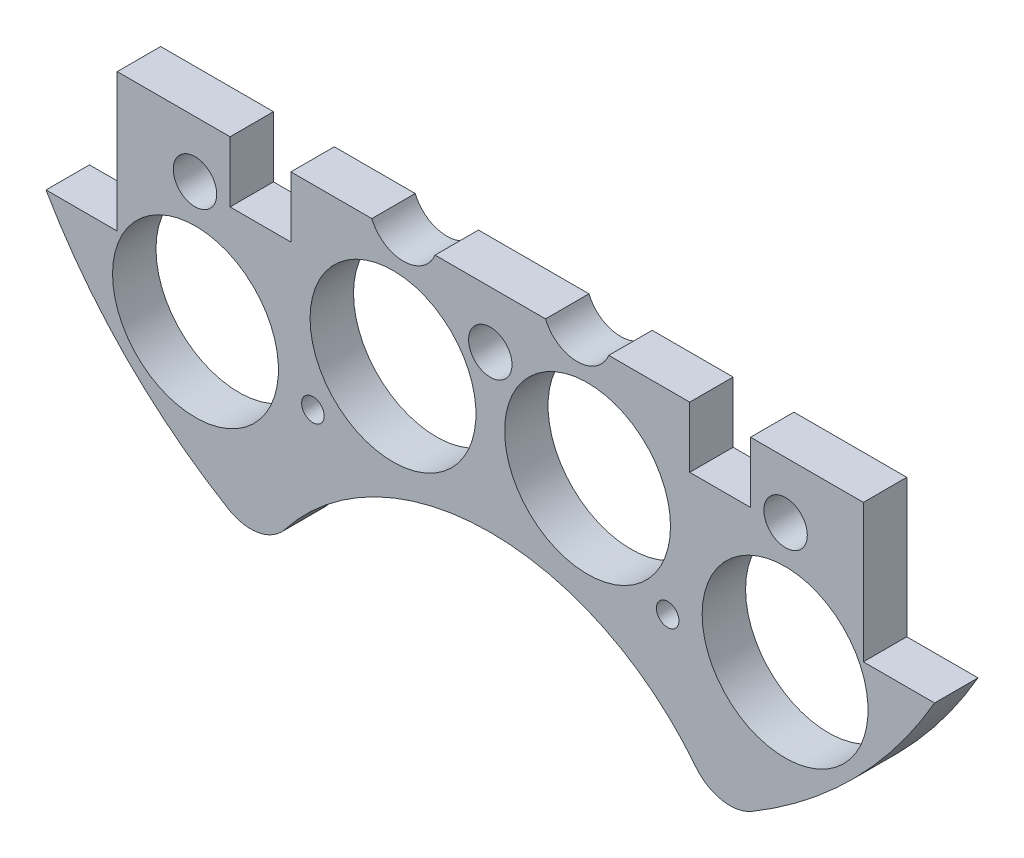
SolidWorks part; units mm, degrees
ref_plane "Front Plane" through (0, 0, 0) normal (0, 0, 1) x (1, 0, 0)
ref_plane "Top Plane" through (0, 0, 0) normal (0, 1, 0) x (1, 0, 0)
ref_plane "Right Plane" through (0, 0, 0) normal (1, 0, 0) x (0, 0, -1)
sketch "Sketch1" plane through (0, 0, 0) normal (0, 0, 1) x (1, 0, 0)
  line L0 (0, 0) -> (-82.1241, 0) construction
  line L1 (0, 0) -> (0, 95.6219) construction
  line L3 (-64.9644, 37.338) -> (-54.5504, 37.338)
  line L5 (-64.9644, -37.338) -> (-54.5504, -37.338)
  line L6 (-54.5504, 37.338) -> (-54.5504, -37.338)
  line L7 (64.9644, -37.338) -> (54.5504, -37.338)
  line L8 (64.9644, 37.338) -> (54.5504, 37.338)
  line L9 (54.5504, 37.338) -> (54.5504, -37.338)
  arc A0 (-64.9644, -37.338) -> (64.9644, -37.338) centre (0, 0) ccw
  circle A1 centre (-46.482, 11.049) radius 1.651
  circle A2 centre (-21.0833, 10.795) radius 1.651
  circle A3 centre (-21.0833, -10.795) radius 1.651
  circle A4 centre (-46.482, -11.049) radius 1.651
  circle A5 centre (46.482, -11.049) radius 1.651
  circle A6 centre (21.0833, -10.795) radius 1.651
  circle A7 centre (21.0833, 10.795) radius 1.651
  circle A8 centre (46.482, 11.049) radius 1.651
  arc A9 (64.9644, 37.338) -> (-64.9644, 37.338) centre (0, 0) ccw
  dimension "D2" = 3.302
  dimension "D3" = 3.302
  dimension "D4" = 25.4
  dimension "D5" = 10.795
  dimension "D10" = 46.482
  dimension "D6" = 74.676
  dimension "D7" = 10.414
  dimension "D8" = 74.93
  dimension "D9" = 74.93
  dimension "D11" = 37.338
extrude "Boss-Extrude2" add sketch "Sketch1" along normal blind 6.35
sketch "Sketch2" plane through (0, 0, 6.35) normal (0, 0, 1) x (1, 0, 0)
  line L0 (0, 68.58) -> (0, 55.88) construction
  line L1 (-9.525, 68.58) -> (9.525, 68.58)
  line L2 (-9.525, 68.58) -> (-9.525, 55.88)
  line L3 (-9.525, 55.88) -> (9.525, 55.88)
  line L4 (9.525, 68.58) -> (9.525, 55.88)
  line L5 (-9.525, 62.23) -> (9.525, 62.23) construction
  arc A0 (64.9644, 37.338) -> (-64.9644, 37.338) centre (0, 0) ccw construction
  circle A1 centre (-21.0833, 10.795) radius 1.651 construction
  circle A2 centre (21.0833, 10.795) radius 1.651 construction
  circle A3 centre (-6.731, 62.23) radius 1.143
  circle A4 centre (6.731, 62.23) radius 1.143
  dimension "D4" = 2.286
  dimension "D5" = 0
  dimension "D6" = 6.731
  dimension "D1" = 19.05
  dimension "D2" = 12.7
  dimension "D3" = 55.88
extrude "Cut-Extrude1" cut sketch "Sketch2" against normal through all contours A3 | A4
sketch "Sketch3" plane through (0, 0, 0) normal (0, 0, -1) x (-1, 0, 0)
  line L0 (0, 0) -> (0, -116.2908) construction
  line L1 (0, 0) -> (-153.8039, 0) construction
  line L2 (0, 0) -> (15.2681, -56.9814) construction
  circle A4 centre (-43.1052, -43.1052) radius 12.1285
  circle A6 centre (14.224, -34.29) radius 12.1285
  circle A7 centre (14.224, 34.29) radius 12.1285
  circle A8 centre (-43.1052, 43.1052) radius 12.1285
  circle A11 centre (43.1052, 43.1052) radius 12.1285
  circle A12 centre (-14.224, 34.29) radius 12.1285
  circle A13 centre (-14.224, -34.29) radius 12.1285
  circle A14 centre (43.1052, -43.1052) radius 12.1285
  point P36 (0, 0)
  point P53 (0, 0)
  point P55 (0, 0)
  dimension "D1" = 14.224
  dimension "D2" = 34.29
  dimension "D4" = 15
  dimension "D8" = 24.257
extrude "Cut-Extrude2" cut sketch "Sketch3" against normal through all
sketch "Sketch4" plane through (0, 0, 0) normal (0, 0, -1) x (-1, 0, 0)
  line L1 (-15.7702, 56.3138) -> (12.7925, 56.3138)
  line L2 (-15.7702, 56.3138) -> (-15.7702, 67.9913)
  line L3 (-15.7702, 67.9913) -> (12.7925, 67.9913)
  line L4 (12.7925, 56.3138) -> (12.7925, 67.9913)
extrude "Boss-Extrude3" add sketch "Sketch4" against normal up to surface (6.35 mm away) up to face at (-55.2337, -43.1052, 6.35)
sketch "Sketch5" plane through (0, 0, 0) normal (0, 0, -1) x (-1, 0, 0)
  line L1 (-85.044, -17.145) -> (131.6774, -17.145)
  line L2 (-85.044, -17.145) -> (-85.044, 113.4242)
  line L3 (-85.044, 113.4242) -> (131.6774, 113.4242)
  line L4 (131.6774, -17.145) -> (131.6774, 113.4242)
  circle A0 centre (-21.0833, -10.795) radius 1.651 construction
  dimension "D1" = 6.35
extrude "Cut-Extrude4" cut sketch "Sketch5" against normal through all contours L2 L3 L4 L1
sketch "Sketch6" plane through (0, 0, 0) normal (0, 0, -1) x (-1, 0, 0)
  line L0 (-33.02, -67.2621) -> (33.02, -67.2621)
  line L1 (0, 0) -> (0, -146.3858) construction
  arc A0 (-64.9644, -37.338) -> (64.9644, -37.338) centre (0, 0) ccw construction
  circle A1 centre (0, -86.3121) radius 38.1
  dimension "D2" = 76.2
  dimension "D1" = 66.04
  dimension "D3" = 19.05
extrude "Cut-Extrude5" cut sketch "Sketch6" against normal blind 60.96 contours A1
extrude "Cut-Extrude6" cut sketch "Sketch7" against normal through all both and the other way through all
sketch "Sketch7" plane through (-31.3134, 132.614, 31.75) normal (0, 0, 1) x (0, 1, 0)
  line L0 (-132.614, -31.3134) -> (-132.614, 57.8454) construction
  line L1 (-132.614, -31.3134) -> (-222.516, -31.3134) construction
  circle A0 centre (-158.014, 14.4066) radius 3.175
  circle A1 centre (-173.254, -31.3134) radius 3.175
  circle A3 centre (-158.014, -77.0334) radius 3.175
  circle A4 centre (-107.214, -77.0334) radius 3.175
  circle A5 centre (-91.974, -31.3134) radius 3.175
  circle A6 centre (-107.214, 14.4066) radius 3.175
fillet "Fillet1" radius 6.35 1 edges at (-33.001, -67.2714, 3.175)
fillet "Fillet2" radius 6.35 1 edges at (33.001, -67.2714, 3.175)
extrude "Cut-Extrude8" cut sketch "Sketch9" against normal blind 29.21
sketch "Sketch9" plane through (-31.3134, 132.559, 28.575) normal (0, 0, 1) x (0, 1, 0)
  line L0 (-132.559, -31.3134) -> (6.1626, -31.3134) construction
  line L2 (-132.559, -31.3134) -> (-132.559, -122.6589) construction
  circle A0 centre (-190.979, 2.9766) radius 1.651
  circle A2 centre (-154.784, -31.3134) radius 1.651
  circle A3 centre (-190.979, -65.6034) radius 1.651
  circle A4 centre (-110.334, -31.3134) radius 1.651
  circle A5 centre (-74.139, -65.6034) radius 1.651
  circle A6 centre (-74.139, 2.9766) radius 1.651
extrude "Cut-Extrude99" cut sketch "Sketch100" against normal blind 29.21
sketch "Sketch100" plane through (-31.3134, 132.559, 22.225) normal (0, 0, 1) x (0, 1, 0)
  line L0 (-143.7712, -34.3645) -> (6.1626, -34.3645) construction
  line L2 (-143.7712, -34.3645) -> (-143.7712, -122.6589) construction
  circle A0 centre (-202.1912, -0.0745) radius 1.651
  circle A2 centre (-165.9962, -34.3645) radius 1.651
  circle A3 centre (-202.1912, -68.6545) radius 1.651
  circle A4 centre (-121.5462, -34.3645) radius 1.651
  circle A5 centre (-85.3512, -68.6545) radius 1.651
  circle A6 centre (-85.3512, -0.0745) radius 1.651
sketch "Sketch102" plane through (0, 0, 0) normal (0, 0, -1) x (-1, 0, 0)
  line L0 (-54.5504, -17.145) -> (54.5504, -17.145) construction
  line L1 (-38.0504, -17.145) -> (-29.1604, -17.145)
  line L2 (-38.0504, -17.145) -> (-38.0504, -26.035)
  line L3 (-38.0504, -26.035) -> (-29.1604, -26.035)
  line L4 (-29.1604, -17.145) -> (-29.1604, -26.035)
  line L5 (0, 15.7454) -> (0, -80.7771) construction
  line L6 (29.1604, -17.145) -> (38.0504, -17.145)
  line L7 (29.1604, -17.145) -> (29.1604, -26.035)
  line L8 (29.1604, -26.035) -> (38.0504, -26.035)
  line L9 (38.0504, -17.145) -> (38.0504, -26.035)
  line L10 (-54.5504, -37.338) -> (-54.5504, -17.145) construction
  dimension "D1" = 8.89
  dimension "D2" = 8.89
  dimension "D3" = 16.5
extrude "Cut-Extrude101" cut sketch "Sketch102" against normal through all
sketch "Sketch105" plane through (0, 0, 0) normal (0, 0, -1) x (-1, 0, 0)
  line L0 (0, 0) -> (0, -99.3188) construction
  circle A0 centre (-12.7, -15.24) radius 5
  circle A1 centre (12.7, -15.24) radius 5
  dimension "D1" = 10
  dimension "D2" = 12.7
  dimension "D3" = 15.24
extrude "Cut-Extrude104" cut sketch "Sketch105" against normal blind 10
extrude "Cut-Extrude105" cut sketch "Sketch106" against normal through all and the other way blind 103.378
sketch "Sketch106" plane through (30.092, 4.0835, 25.4) normal (0, 0, -1) x (-1, 0, 0)
  line L0 (30.092, -4.0835) -> (148.6336, -4.0835) construction
  line L1 (30.092, -4.0835) -> (30.092, 90.452) construction
  circle A0 centre (-13.088, 21.3165) radius 3.175
  circle A1 centre (73.272, 21.3165) radius 3.175
  circle A2 centre (30.092, 21.3165) radius 3.175
  circle A4 centre (73.272, -29.4835) radius 3.175
  circle A5 centre (30.092, -29.4835) radius 3.175
  circle A6 centre (-13.088, -29.4835) radius 3.175
extrude "Cut-Extrude157" cut sketch "Sketch158" against normal blind 97.79
sketch "Sketch158" plane through (30.092, 4.0835, -22.225) normal (0, 0, -1) x (-1, 0, 0)
  line L0 (30.092, -29.4835) -> (30.092, 6.2385) construction
  circle A0 centre (4.1544, -49.7288) radius 1.651
  circle A4 centre (56.0296, -49.7288) radius 1.651
  circle A5 centre (4.1544, 41.3825) radius 1.651
  circle A9 centre (56.0296, 41.3825) radius 1.651
